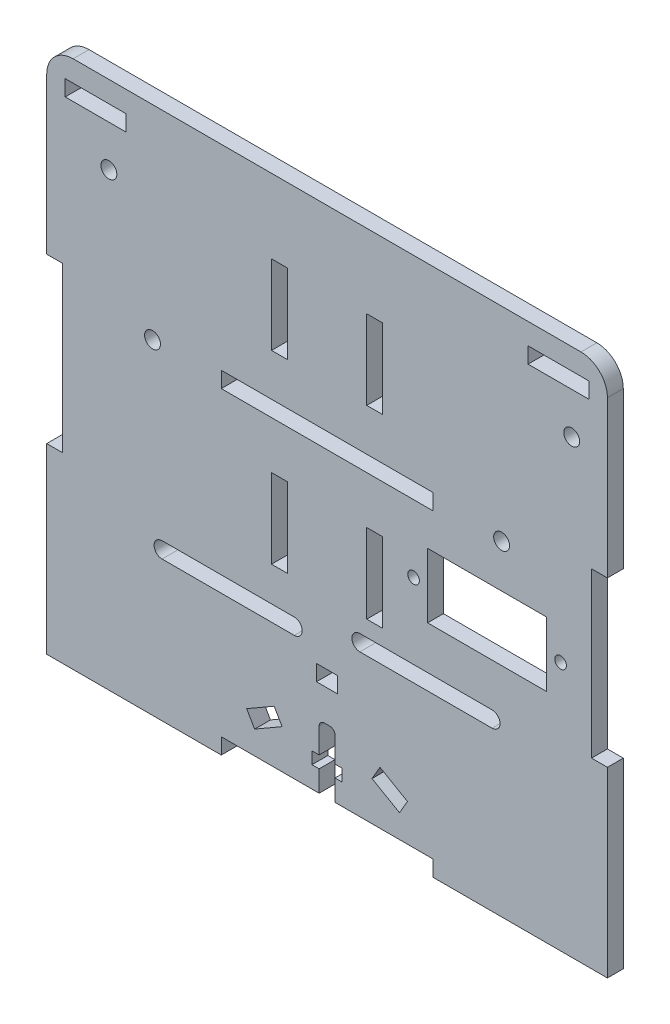
SolidWorks part; units mm, degrees
other "Marcação1"
sketch "Esboço7" plane through (-68, 31.5, 3) normal (-0.6758, 0.2828, 0.6807) x (0.7271, 0.1043, 0.6785)
sketch "Esboço8" plane through (-68, 31.5, 3) normal (-0.6758, 0.2828, 0.6807) x (0.7271, 0.1043, 0.6785)
sketch "Esboço9" plane through (-60.5, 31.5, 3) normal (-0.6758, 0.2828, 0.6807) x (0.7271, 0.1043, 0.6785)
sketch "Esboço11" plane through (-60.5, 31.5, 3) normal (-0.6758, 0.2828, 0.6807) x (0.7271, 0.1043, 0.6785)
sketch "Esboço13" plane through (-60.5, 36.25, 3) normal (-0.6758, 0.2828, 0.6807) x (0.7271, 0.1043, 0.6785)
sketch "Esboço14" plane through (-60.5, 36.25, 3) normal (-0.6758, 0.2828, 0.6807) x (0.7271, 0.1043, 0.6785)
sketch "Esboço17" plane through (-60.5, 36.25, 3) normal (-0.6758, 0.2828, 0.6807) x (0.7271, 0.1043, 0.6785)
sketch "Esboço18" plane through (-60.5, 51.25, 3) normal (-0.6758, 0.2828, 0.6807) x (0.7271, 0.1043, 0.6785)
sketch "Esboço19" plane through (-60.5, 51.25, 3) normal (-0.6758, 0.2828, 0.6807) x (0.7271, 0.1043, 0.6785)
sketch "Esboço20" plane through (-60.5, 51.25, 3) normal (-0.6758, 0.2828, 0.6807) x (0.7271, 0.1043, 0.6785)
sketch "Sketch9" plane through (-53, 50, 1.5) normal (-0.6758, 0.2828, 0.6807) x (0.7271, 0.1043, 0.6785)
sketch "Sketch10" plane through (-53, 50, 1.5) normal (-0.6758, 0.2828, 0.6807) x (0.7271, 0.1043, 0.6785)
material "Acrylic (Medium-high impact)"
ref_plane "Plano frontal" through (0, 0, 0) normal (0, 0, 1) x (1, 0, 0)
ref_plane "Plano superior" through (0, 0, 0) normal (0, 1, 0) x (1, 0, 0)
ref_plane "Plano direito" through (0, 0, 0) normal (1, 0, 0) x (0, 0, -1)
sketch "Esboço1" plane through (0, 0, 0) normal (0, 0, 1) x (1, 0, 0)
  line L1 (-50, -50) -> (50, -50)
  line L2 (-50, -50) -> (-50, 50)
  line L3 (-50, 50) -> (50, 50)
  line L4 (50, -50) -> (50, 50)
  line L5 (-50, -50) -> (50, 50) construction
  line L6 (-50, 50) -> (50, -50) construction
  point P0 (0, 0)
  dimension "D1" = 100
  dimension "D2" = 100
extrude "Ressalto-extrusão1" add sketch "Esboço1" along normal mid plane 3
sketch "Esboço2" plane through (0, 0, 1.5) normal (0, 0, 1) x (1, 0, 0)
  line L1 (-20, -50) -> (20, -50)
  line L2 (-20, -50) -> (-20, -47)
  line L3 (-20, -47) -> (20, -47)
  line L4 (20, -50) -> (20, -47)
  line L6 (-50, -50) -> (50, -50) construction
  line L7 (0, -1.65) -> (0, 1.65) construction
  line L15 (50, 50) -> (-50, 50) construction
  line L21 (-20, 13) -> (20, 13)
  line L22 (-20, 13) -> (-20, 10)
  line L23 (-20, 10) -> (20, 10)
  line L24 (20, 13) -> (20, 10)
  line L25 (-20, 13) -> (20, 10) construction
  line L26 (-20, 10) -> (20, 13) construction
  circle A2 centre (-33, 11.5) radius 1.5
  circle A4 centre (33, 11.5) radius 1.5
  point P6 (0, -47)
  point P14 (0, 11.5)
  dimension "D4" = 3
  dimension "D8" = 3
  dimension "D5" = 13
  dimension "D2" = 40
  dimension "D3" = 37
  dimension "D6" = 3
  dimension "D13" = 40
extrude "Corte-extrusão1" cut sketch "Esboço2" against normal through all
sketch "Esboço3" plane through (0, 0, 1.5) normal (0, 0, 1) x (1, 0, 0)
  line L0 (-50, 50) -> (-50, -50) construction
  line L1 (-50, -15.5) -> (-53, -15.5)
  line L2 (-50, -15.5) -> (-50, -50)
  line L3 (-50, -50) -> (-53, -50)
  line L4 (-53, -15.5) -> (-53, -50)
  line L5 (0, -1.65) -> (0, 1.65) construction
  line L6 (50, -50) -> (53, -50)
  line L7 (50, -15.5) -> (53, -15.5)
  line L8 (50, -15.5) -> (50, -50)
  line L9 (53, -15.5) -> (53, -50)
  line L10 (-50, -50) -> (-20, -50) construction
  line L11 (50, 50) -> (-50, 50) construction
  line L16 (-53, 15.5) -> (-53, 50)
  line L17 (-50, 50) -> (-53, 50)
  line L18 (-50, 15.5) -> (-50, 50)
  line L19 (-50, 15.5) -> (-53, 15.5)
  line L20 (50, -50) -> (50, 50) construction
  line L21 (50, 15.5) -> (53, 15.5)
  line L22 (50, 15.5) -> (50, 50)
  line L23 (50, 50) -> (53, 50)
  line L24 (53, 15.5) -> (53, 50)
  line L25 (93.1741, 0) -> (-93.1741, 0) construction
  line L26 (0, -62.7565) -> (0, 62.7565) construction
  point P31 (0, 0)
  point P38 (0, 0)
  dimension "D1" = 3
  dimension "D2" = 31
  dimension "D4" = 3
  dimension "D5" = 53
extrude "Ressalto-extrusão2" add sketch "Esboço3" against normal through all
sketch "Sketch2" plane through (0, 0, 0) normal (0, 0, 1) x (1, 0, 0)
  line L0 (20, -47) -> (-20, -47) construction
  line L1 (-0.5, -35) -> (0.5, -35)
  line L2 (-1.5, -36) -> (-1.5, -40.73)
  line L3 (-1.5, -47) -> (1.5, -47)
  line L4 (1.5, -36) -> (1.5, -40.73)
  line L5 (1.5, -40.73) -> (2.85, -40.73)
  line L6 (-2.85, -40.73) -> (-1.5, -40.73)
  line L7 (-2.85, -40.73) -> (-2.85, -43)
  line L8 (-2.85, -43) -> (-1.5, -43)
  line L9 (2.85, -40.73) -> (2.85, -43)
  line L10 (-1.5, -43) -> (-1.5, -47)
  line L11 (1.5, -43) -> (2.85, -43)
  line L12 (1.5, -43) -> (1.5, -47)
  arc A0 (0.5, -35) -> (1.5, -36) centre (0.5, -36) cw
  arc A1 (-0.5, -35) -> (-1.5, -36) centre (-0.5, -36) ccw
  point P6 (0, -35)
  point P18 (1.5, -35)
  point P21 (-1.5, -35)
  dimension "D7" = 1
  dimension "D1" = 3
  dimension "D2" = 12
  dimension "D3" = 2.27
  dimension "D4" = 1.35
  dimension "D5" = 1.35
  dimension "D6" = 4
extrude "Cut-Extrude4" cut sketch "Sketch2" against normal through all both and the other way through all
fillet "Fillet1" radius 5 2 edges at (53, 50, 0) (-53, 50, 0)
sketch "Sketch3" plane through (0, 0, 0) normal (0, 0, 1) x (1, 0, 0)
  line L0 (7.5, 1) -> (7.5, -14)
  line L1 (10.5, 36) -> (7.5, 36)
  line L2 (10.5, 36) -> (10.5, 21)
  line L3 (10.5, 21) -> (7.5, 21)
  line L4 (7.5, 36) -> (7.5, 21)
  line L6 (0, -1.65) -> (0, 1.65) construction
  line L7 (-7.5, 36) -> (-7.5, 21)
  line L8 (-10.5, 21) -> (-7.5, 21)
  line L9 (-10.5, 36) -> (-10.5, 21)
  line L10 (-10.5, 36) -> (-7.5, 36)
  line L11 (-10.5, 1) -> (-7.5, 1)
  line L12 (48, 50) -> (-48, 50) construction
  line L28 (-2, -26) -> (2, -26)
  line L29 (-2, -26) -> (-2, -29)
  line L30 (-2, -29) -> (2, -29)
  line L31 (2, -26) -> (2, -29)
  line L32 (-10.5, 1) -> (-10.5, -14)
  line L33 (-10.5, -14) -> (-7.5, -14)
  line L34 (-7.5, 1) -> (-7.5, -14)
  line L35 (10.5, -14) -> (7.5, -14)
  line L36 (10.5, 1) -> (10.5, -14)
  line L37 (10.5, 1) -> (7.5, 1)
  line L40 (-15.1962, -40) -> (-10, -37)
  line L41 (-15.1962, -40) -> (-13.6962, -42.5981)
  line L42 (-13.6962, -42.5981) -> (-8.5, -39.5981)
  line L43 (-10, -37) -> (-8.5, -39.5981)
  line L45 (-1.5, -47) -> (-20, -47) construction
  line L46 (10, -37) -> (8.5, -39.5981)
  line L47 (13.6962, -42.5981) -> (8.5, -39.5981)
  line L48 (15.1962, -40) -> (13.6962, -42.5981)
  line L49 (15.1962, -40) -> (10, -37)
  point P4 (0, -26)
  point P30 (0, -29)
  dimension "D1" = 3
  dimension "D2" = 15
  dimension "D3" = 12
  dimension "D4" = 3
  dimension "D5" = 14
  dimension "D6" = 6
  dimension "D7" = 4
  dimension "D8" = 20
  dimension "D9" = 15
  dimension "D10" = 30
  dimension "D12" = 4.4019
  dimension "D13" = 8
  dimension "D14" = 10
extrude "Cut-Extrude5" cut sketch "Sketch3" against normal through all both and the other way through all
sketch "Sketch1" plane through (0, 0, -1.5) normal (0, 0, -1) x (-1, 0, 0)
  line L1 (53, 45) -> (53, 15.5) construction
  line L22 (0, 1.65) -> (0, -1.65) construction
  line L28 (-53, 15.5) -> (-53, 45) construction
  line L30 (-48, 50) -> (48, 50) construction
  line L32 (-20, 13) -> (20, 13) construction
  line B0 (-46.5, 42.5307) -> (-46.4957, 42.5307)
  line B1 (-50, 34.5307) -> (-50, 28.5307)
  line B2 (-48, 26.5307) -> (-46.4957, 26.5307)
  line B3 (-37, 40.5307) -> (-37, 28.5307)
  line B4 (-50, 34.5307) -> (-37, 34.5307) construction
  line B5 (-40.36, 44.2807) -> (-41.93, 47)
  line B6 (-41.93, 47) -> (-45.07, 47)
  line B7 (-45.07, 47) -> (-46.64, 44.2807)
  line B8 (-46.64, 44.2807) -> (-46.0626, 43.2807)
  line B9 (-40.9374, 43.2807) -> (-40.36, 44.2807)
  line B10 (-40.5043, 42.5307) -> (-39, 42.5307)
  line B11 (-40.9374, 25.7807) -> (-40.36, 24.7807)
  line B12 (-46.64, 24.7807) -> (-46.0626, 25.7807)
  line B13 (-45.07, 22.0614) -> (-46.64, 24.7807)
  line B14 (-41.93, 22.0614) -> (-45.07, 22.0614)
  line B15 (-40.36, 24.7807) -> (-41.93, 22.0614)
  line B16 (-40.5043, 26.5307) -> (-39, 26.5307)
  arc B17 (-41.145, 42.921) -> (-45.855, 42.921) centre (-43.5, 44.2807) ccw construction
  arc B18 (-41.145, 26.1403) -> (-45.855, 26.1403) centre (-43.5, 24.7807) cw construction
  arc B19 (-40.9374, 25.7807) -> (-40.5043, 26.5307) centre (-40.5043, 26.0307) cw
  arc B20 (-46.0626, 25.7807) -> (-46.4957, 26.5307) centre (-46.4957, 26.0307) ccw
  arc B21 (-40.5043, 42.5307) -> (-40.9374, 43.2807) centre (-40.5043, 43.0307) cw
  arc B22 (-46.4957, 42.5307) -> (-46.0626, 43.2807) centre (-46.4957, 43.0307) ccw
  arc B23 (-39, 42.5307) -> (-37, 40.5307) centre (-39, 40.5307) cw
  arc B24 (-39, 26.5307) -> (-37, 28.5307) centre (-39, 28.5307) ccw
  arc B25 (-50, 28.5307) -> (-48, 26.5307) centre (-48, 28.5307) ccw
  arc B26 (-48, 42.5307) -> (-50, 40.5307) centre (-48, 40.5307) ccw
  line B27 (-50, 40.5307) -> (-50, 34.5307)
  line B28 (-48, 42.5307) -> (-46.5, 42.5307)
  line B29 (46.5, 42.5307) -> (46.4957, 42.5307)
  line B30 (50, 34.5307) -> (50, 28.5307)
  line B31 (48, 26.5307) -> (46.4957, 26.5307)
  line B32 (37, 40.5307) -> (37, 28.5307)
  line B33 (50, 34.5307) -> (37, 34.5307) construction
  line B34 (40.36, 44.2807) -> (41.93, 47)
  line B35 (41.93, 47) -> (45.07, 47)
  line B36 (45.07, 47) -> (46.64, 44.2807)
  line B37 (46.64, 44.2807) -> (46.0626, 43.2807)
  line B38 (40.9374, 43.2807) -> (40.36, 44.2807)
  line B39 (40.5043, 42.5307) -> (39, 42.5307)
  line B40 (40.9374, 25.7807) -> (40.36, 24.7807)
  line B41 (46.64, 24.7807) -> (46.0626, 25.7807)
  line B42 (45.07, 22.0614) -> (46.64, 24.7807)
  line B43 (41.93, 22.0614) -> (45.07, 22.0614)
  line B44 (40.36, 24.7807) -> (41.93, 22.0614)
  line B45 (40.5043, 26.5307) -> (39, 26.5307)
  arc B46 (41.145, 42.921) -> (45.855, 42.921) centre (43.5, 44.2807) cw construction
  arc B47 (41.145, 26.1403) -> (45.855, 26.1403) centre (43.5, 24.7807) ccw construction
  arc B48 (40.9374, 25.7807) -> (40.5043, 26.5307) centre (40.5043, 26.0307) ccw
  arc B49 (46.0626, 25.7807) -> (46.4957, 26.5307) centre (46.4957, 26.0307) cw
  arc B50 (40.5043, 42.5307) -> (40.9374, 43.2807) centre (40.5043, 43.0307) ccw
  arc B51 (46.4957, 42.5307) -> (46.0626, 43.2807) centre (46.4957, 43.0307) cw
  arc B52 (39, 42.5307) -> (37, 40.5307) centre (39, 40.5307) ccw
  arc B53 (39, 26.5307) -> (37, 28.5307) centre (39, 28.5307) cw
  arc B54 (50, 28.5307) -> (48, 26.5307) centre (48, 28.5307) cw
  arc B55 (48, 42.5307) -> (50, 40.5307) centre (48, 40.5307) cw
  line B56 (50, 40.5307) -> (50, 34.5307)
  line B57 (48, 42.5307) -> (46.5, 42.5307)
  dimension "D1" = 3
  dimension "D2" = 9.0614
  dimension "D3" = 3
sketch_block_instance "Gy Cortado-1"
sketch_block "Gy Cortado" parameters "D3"=0.5, "D4"=2, "D5"=0.5, "D1"=3.14, "D2"=19.5
sketch_block_instance "Gy Cortado-3"
extrude "Corte Gy-VL53L0" [suppressed] cut sketch "Sketch1" against normal through all both and the other way through all
sketch "Sketch8" plane through (0, 0, 0) normal (0, 0, 1) x (1, 0, 0)
  line L0 (-53, 45) -> (-53, 15.5) construction
  line L1 (-49.5, 46) -> (-38, 46)
  line L2 (-49.5, 46) -> (-49.5, 43)
  line L3 (-49.5, 43) -> (-38, 43)
  line L4 (-38, 46) -> (-38, 43)
  line L6 (0, -1.65) -> (0, 1.65) construction
  line L7 (38, 46) -> (38, 43)
  line L8 (49.5, 43) -> (38, 43)
  line L9 (49.5, 46) -> (49.5, 43)
  line L10 (49.5, 46) -> (38, 46)
  line L11 (48, 50) -> (-48, 50) construction
  circle A0 centre (-41.25, 35.2) radius 1.5
  circle A1 centre (46.25, 35.2) radius 1.5
  arc A4 (-48, 50) -> (-53, 45) centre (-48, 45) ccw construction
  point P6 (-43.75, 43)
  point P22 (43.75, 43)
  dimension "D3" = 3
  dimension "D7" = 4
  dimension "D1" = 11.5
  dimension "D2" = 7.8
  dimension "D4" = 3
  dimension "D5" = 3.5
  dimension "D6" = 2.5
  dimension "D8" = 2.5
  dimension "D9" = 3.1972
extrude "Corte GY-53LDK" cut sketch "Sketch8" against normal through all both and the other way through all
sketch "Sketch4" plane through (0, 0, 1.5) normal (0, 0, 1) x (1, 0, 0)
  line L0 (41.5, 2.5) -> (41.5, -1.188) construction
  line L1 (19, 3.35) -> (41.5, 3.35)
  line L2 (19, 3.35) -> (19, -8.85)
  line L3 (19, -8.85) -> (41.5, -8.85)
  line L4 (41.5, 3.35) -> (41.5, -8.85)
  line L5 (19, -8) -> (19, 2.5) construction
  line L6 (19.85, 3.35) -> (33.838, 3.35) construction
  line L9 (33.838, -8.85) -> (19.85, -8.85) construction
  circle A0 centre (44.15, -2.75) radius 1.1
  circle A1 centre (16.35, -2.75) radius 1.1
  dimension "D1" = 2.2
extrude "Cut-Extrude6" cut sketch "Sketch4" against normal through all both and the other way through all
sketch "Sketch6" plane through (0, 0, 1.5) normal (0, 0, 1) x (1, 0, 0)
  line L0 (-31.2, -22) -> (-6.2, -22) construction
  line L4 (-31.2, -20.5) -> (-6.2, -20.5)
  line L6 (-20.3081, -20.2) -> (-20.3081, -23.8) construction
  line L8 (-31.2, -23.5) -> (-6.2, -23.5)
  line L11 (6.2, -18.5) -> (31.2, -18.5) construction
  line L12 (6.2, -17) -> (31.2, -17)
  line L13 (6.2, -20) -> (31.2, -20)
  line L15 (17.0919, -16.7) -> (17.0919, -20.3) construction
  line L16 (50, -15.5) -> (50, 15.5) construction
  circle A4 centre (-20.3081, -22) radius 1.8 construction
  circle A5 centre (17.0919, -18.5) radius 1.8 construction
  arc A9 (-31.2, -20.5) -> (-31.2, -23.5) centre (-31.2, -22) ccw
  arc A10 (-6.2, -23.5) -> (-6.2, -20.5) centre (-6.2, -22) ccw
  arc A12 (6.2, -17) -> (6.2, -20) centre (6.2, -18.5) ccw
  arc A13 (31.2, -20) -> (31.2, -17) centre (31.2, -18.5) ccw
  point P2 (-18.7, -22)
  point P9 (18.7, -18.5)
  point P14 (-20.3081, -22)
  point P27 (17.0919, -18.5)
  dimension "D3" = 12.4
  dimension "D2" = 18.8
  dimension "D6" = 25
  dimension "D1" = 3
extrude "Cut-Extrude7" cut sketch "Sketch6" against normal through all both and the other way through all
